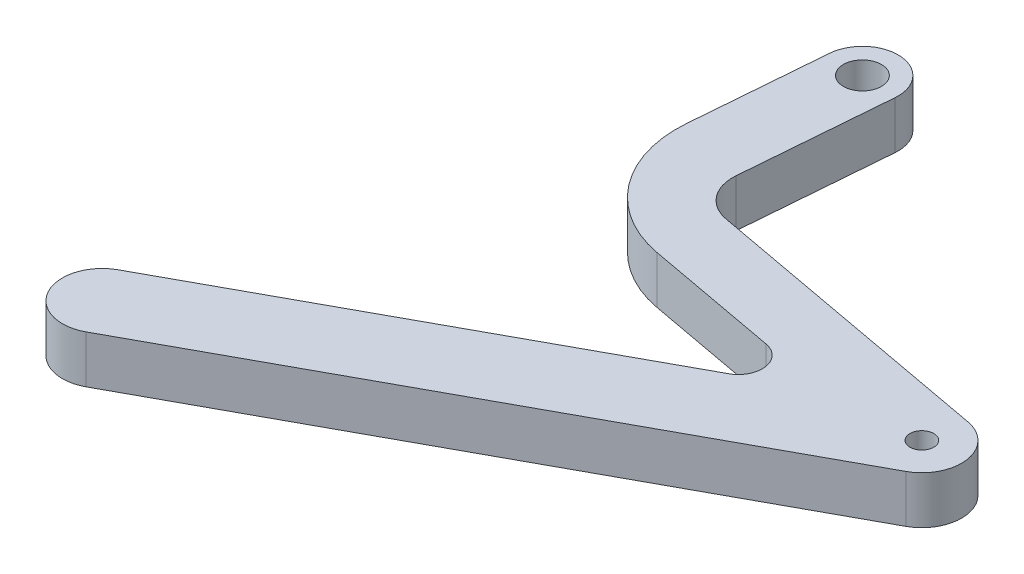
SolidWorks part; units mm, degrees
ref_plane "Front Plane" through (0, 0, 0) normal (0, 0, 1) x (1, 0, 0)
ref_plane "Top Plane" through (0, 0, 0) normal (0, 1, 0) x (1, 0, 0)
ref_plane "Right Plane" through (0, 0, 0) normal (1, 0, 0) x (0, 0, -1)
sketch "Sketch1" plane through (0, 0, 0) normal (0, 1, 0) x (1, 0, 0)
  line L10 (-19.4361, 35.9212) -> (-20.7845, 19.2505)
  line L11 (-8.5548, 3.2902) -> (8.3038, 0.1798)
  line L12 (9.1944, -5.405) -> (-40.652, -32.5534)
  line L13 (-35.869, -41.3354) -> (31.0124, -4.9091)
  line L14 (29.5281, 4.3989) -> (-7.8911, 11.3027)
  line L15 (-11.9676, 16.6228) -> (-10.4654, 35.1956)
  circle A37 centre (28.6209, -0.5181) radius 1.5
  circle A38 centre (-14.9508, 35.5584) radius 2.4
  arc A39 (-10.4654, 35.1956) -> (-19.4361, 35.9212) centre (-14.9508, 35.5584) ccw
  arc A40 (-20.7845, 19.2505) -> (-8.5548, 3.2902) centre (-5.8333, 18.0412) ccw
  arc A41 (9.1944, -5.405) -> (8.3038, 0.1798) centre (7.7595, -2.7704) ccw
  arc A42 (-40.652, -32.5534) -> (-35.869, -41.3354) centre (-38.2605, -36.9444) ccw
  arc A43 (31.0124, -4.9091) -> (29.5281, 4.3989) centre (28.6209, -0.5181) ccw
  arc A44 (-11.9676, 16.6228) -> (-7.8911, 11.3027) centre (-6.9839, 16.2197) ccw
  dimension "D2" = 3
  dimension "D1" = 4.8
extrude "Boss-Extrude1" add sketch "Sketch1" along normal blind 6
